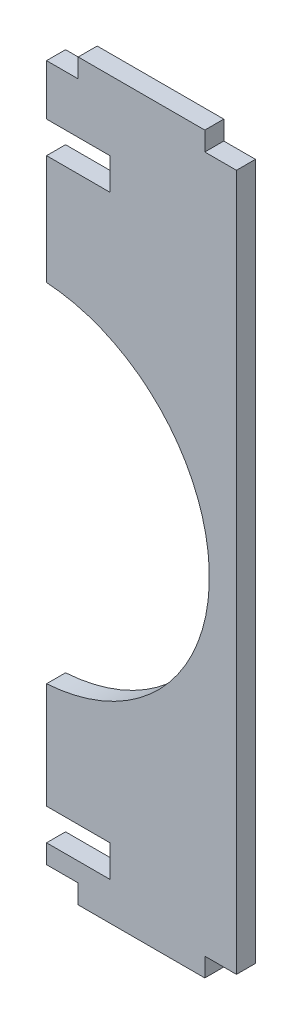
SolidWorks part; units mm, degrees
ref_plane "Front Plane" through (0, 0, 0) normal (0, 0, 1) x (1, 0, 0)
ref_plane "Top Plane" through (0, 0, 0) normal (0, 1, 0) x (1, 0, 0)
ref_plane "Right Plane" through (0, 0, 0) normal (1, 0, 0) x (0, 0, -1)
sketch "Sketch1" plane through (0, 0, 0) normal (0, 0, 1) x (1, 0, 0)
  line L0 (-5, 0) -> (-5, -3)
  line L1 (-5, -3) -> (-5, 0) construction
  line L2 (-5, 0) -> (-5, -3) construction
  line L3 (-4.65, -116) -> (-9.25, -116) construction
  line L4 (-5, -116) -> (-25, -116)
  line L5 (-25, -116) -> (-25, -113)
  line L7 (-25, -113) -> (-30, -113)
  line L8 (-75, -113) -> (-28.3461, -113) construction
  line L9 (-30, -113) -> (-30, -88.2435)
  line L10 (-5, 0) -> (-25, 0)
  line L11 (-25, 0) -> (-5, 0) construction
  line L12 (-25, 0) -> (-25, -3)
  line L13 (-28.3461, -3) -> (-23, -3) construction
  line L14 (-25, -3) -> (-5, -3) construction
  line L15 (-25, -3) -> (-30, -3)
  line L16 (-30, -3) -> (-30, -33.359)
  line L17 (-5, -3) -> (0, -3)
  line L18 (0, -3) -> (0, -113.0082)
  line L19 (0, -113.0082) -> (-5, -113.0082)
  line L20 (-5, -113.0082) -> (-5, -116)
  arc A0 (-30, -88.2435) -> (-30, -33.359) centre (-31.7807, -60.8012) ccw
  point P11 (0, 0)
  point P12 (7.853, -105.5641)
  point P17 (13.3291, -101.2294)
  dimension "D1" = 55
  dimension "D2" = 30
  dimension "D3" = 20
  dimension "D4" = 20
  dimension "D5" = 5
extrude "Boss-Extrude1" add sketch "Sketch1" along normal blind 3
sketch "Sketch2" plane through (0, 0, 3) normal (0, 0, 1) x (1, 0, 0)
  line L0 (-30, -88.2435) -> (-30, -113) construction
  line L1 (-30, -110) -> (-20, -110)
  line L2 (-30, -110) -> (-30, -105)
  line L3 (-30, -105) -> (-20, -105)
  line L4 (-20, -110) -> (-20, -105)
  line L5 (-10.5933, -109) -> (-53.2075, -109) construction
  line L6 (-30, -3) -> (-30, -33.359) construction
  line L7 (-30, -16) -> (-20, -16)
  line L8 (-30, -16) -> (-30, -11)
  line L9 (-30, -11) -> (-20, -11)
  line L10 (-20, -16) -> (-20, -11)
  line L11 (-10.5933, -12) -> (-53.2075, -12) construction
  dimension "D1" = 5
  dimension "D2" = 1
  dimension "D3" = 10
  dimension "D4" = 5
  dimension "D5" = 1
extrude "Cut-Extrude1" cut sketch "Sketch2" against normal blind 3
